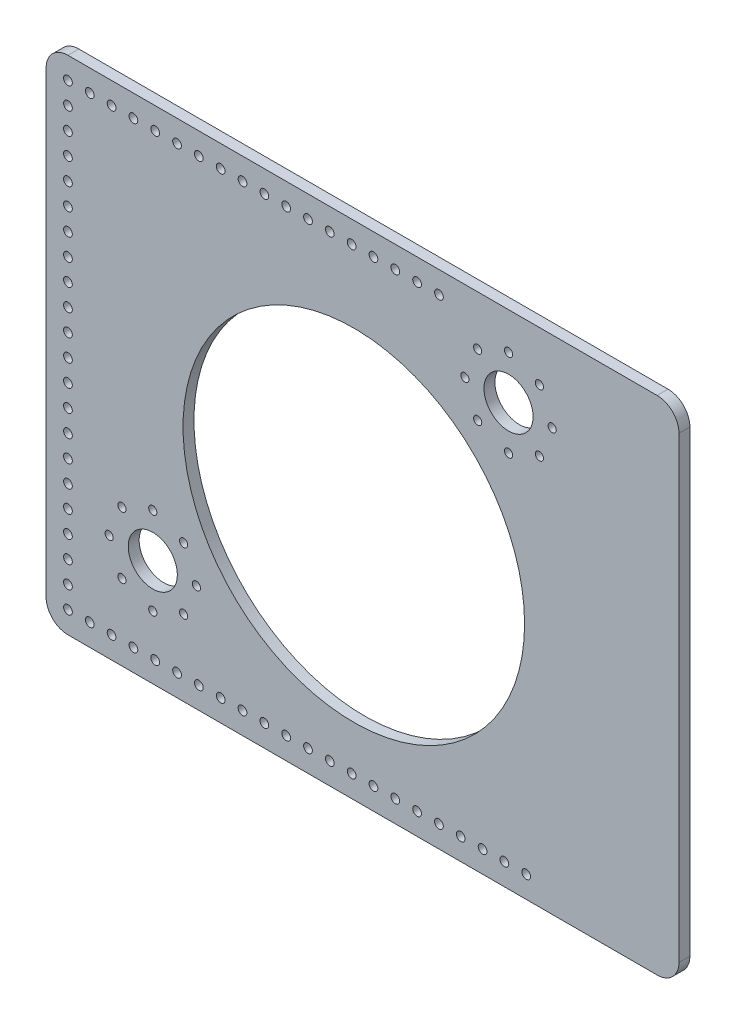
SolidWorks part; units mm, degrees
material "PC High Viscosity"
ref_plane "Front Plane" through (0, 0, 0) normal (0, 0, 1) x (1, 0, 0)
ref_plane "Top Plane" through (0, 0, 0) normal (0, 1, 0) x (1, 0, 0)
ref_plane "Right Plane" through (0, 0, 0) normal (1, 0, 0) x (0, 0, -1)
sketch "Sketch1" plane through (0, 0, 0) normal (0, 0, 1) x (1, 0, 0)
  line L1 (0, 0) -> (368.3, 0)
  line L2 (0, 0) -> (0, 292.1)
  line L4 (368.3, 0) -> (368.3, 292.1)
  line L5 (0, 292.1) -> (368.3, 292.1)
  circle A0 centre (179.07, 138.43) radius 99.3775
  circle A1 centre (12.7, 279.4) radius 2.54
  circle A2 centre (25.4, 279.4) radius 2.54
  circle A3 centre (38.1, 279.4) radius 2.54
  circle A4 centre (50.8, 279.4) radius 2.54
  circle A5 centre (63.5, 279.4) radius 2.54
  circle A6 centre (76.2, 279.4) radius 2.54
  circle A7 centre (88.9, 279.4) radius 2.54
  circle A8 centre (101.6, 279.4) radius 2.54
  circle A9 centre (114.3, 279.4) radius 2.54
  circle A10 centre (127, 279.4) radius 2.54
  circle A11 centre (139.7, 279.4) radius 2.54
  circle A12 centre (152.4, 279.4) radius 2.54
  circle A13 centre (165.1, 279.4) radius 2.54
  circle A14 centre (177.8, 279.4) radius 2.54
  circle A15 centre (190.5, 279.4) radius 2.54
  circle A16 centre (203.2, 279.4) radius 2.54
  circle A17 centre (215.9, 279.4) radius 2.54
  circle A18 centre (228.6, 279.4) radius 2.54
  circle A24 centre (12.7, 266.7) radius 2.54
  circle A25 centre (12.7, 254) radius 2.54
  circle A26 centre (12.7, 241.3) radius 2.54
  circle A27 centre (12.7, 228.6) radius 2.54
  circle A28 centre (12.7, 215.9) radius 2.54
  circle A29 centre (12.7, 203.2) radius 2.54
  circle A30 centre (12.7, 190.5) radius 2.54
  circle A31 centre (12.7, 177.8) radius 2.54
  circle A32 centre (12.7, 165.1) radius 2.54
  circle A33 centre (12.7, 152.4) radius 2.54
  circle A34 centre (12.7, 139.7) radius 2.54
  circle A35 centre (12.7, 127) radius 2.54
  circle A36 centre (12.7, 114.3) radius 2.54
  circle A37 centre (12.7, 101.6) radius 2.54
  circle A38 centre (12.7, 88.9) radius 2.54
  circle A39 centre (12.7, 76.2) radius 2.54
  circle A40 centre (12.7, 63.5) radius 2.54
  circle A41 centre (12.7, 50.8) radius 2.54
  circle A42 centre (12.7, 38.1) radius 2.54
  circle A43 centre (12.7, 25.4) radius 2.54
  circle A44 centre (12.7, 12.7) radius 2.54
  circle A45 centre (25.4, 12.7) radius 2.54
  circle A46 centre (38.1, 12.7) radius 2.54
  circle A47 centre (50.8, 12.7) radius 2.54
  circle A48 centre (63.5, 12.7) radius 2.54
  circle A49 centre (76.2, 12.7) radius 2.54
  circle A50 centre (88.9, 12.7) radius 2.54
  circle A51 centre (101.6, 12.7) radius 2.54
  circle A52 centre (114.3, 12.7) radius 2.54
  circle A53 centre (127, 12.7) radius 2.54
  circle A54 centre (139.7, 12.7) radius 2.54
  circle A55 centre (152.4, 12.7) radius 2.54
  circle A56 centre (165.1, 12.7) radius 2.54
  circle A57 centre (177.8, 12.7) radius 2.54
  circle A58 centre (190.5, 12.7) radius 2.54
  circle A59 centre (203.2, 12.7) radius 2.54
  circle A60 centre (215.9, 12.7) radius 2.54
  circle A61 centre (228.6, 12.7) radius 2.54
  circle A62 centre (241.3, 12.7) radius 2.54
  circle A63 centre (254, 12.7) radius 2.54
  circle A64 centre (266.7, 12.7) radius 2.54
  circle A65 centre (279.4, 12.7) radius 2.54
  dimension "D3" = 198.755
  dimension "D4" = 5.08
  dimension "D5" = 12.7
  dimension "D11" = 12.7
  dimension "D12" = 266.7
  dimension "D14" = 292.1
  dimension "D15" = 12.7
  dimension "D2" = 138.43
  dimension "D6" = 12.7
  dimension "D7" = 368.3
  dimension "D8" = 18
  dimension "D9" = 22
  dimension "D10" = 22
  dimension "D13" = 189.23
extrude "Boss-Extrude1" add sketch "Sketch1" along normal blind 6.35
sketch "Sketch2" plane through (0, 0, 6.35) normal (0, 0, 1) x (1, 0, 0)
  line L0 (177.2452, 140.4926) -> (-32620.0354, 37211.0747) construction
  line L1 (62.0797, 62.0797) -> (0, 62.0797) construction
  line L2 (62.0797, 62.0797) -> (62.0797, 0) construction
  line L3 (62.0797, 0) -> (0, 0) construction
  line L4 (0, 62.0797) -> (0, 0) construction
  line L5 (368.3, 292.1) -> (0, 292.1) construction
  circle A0 centre (62.0797, 62.0797) radius 14.2875
  circle A2 centre (179.07, 138.43) radius 127 construction
  circle A4 centre (62.0797, 62.0797) radius 12.7 construction
  circle A5 centre (269.1087, 245.2435) radius 14.2875
  circle A6 centre (62.0797, 62.0797) radius 25.4 construction
  circle A7 centre (62.0797, 87.4797) radius 2.3812
  circle A8 centre (80.0402, 80.0402) radius 2.3813
  circle A9 centre (87.4797, 62.0797) radius 2.3813
  circle A10 centre (80.0402, 44.1192) radius 2.3813
  circle A11 centre (62.0797, 36.6797) radius 2.3812
  circle A12 centre (44.1192, 44.1192) radius 2.3812
  circle A13 centre (36.6797, 62.0797) radius 2.3812
  circle A14 centre (44.1192, 80.0402) radius 2.3812
  circle A15 centre (269.1087, 245.2435) radius 25.4 construction
  circle A16 centre (269.1087, 270.6435) radius 2.3813
  circle A17 centre (287.0692, 263.204) radius 2.3813
  circle A18 centre (294.5087, 245.2435) radius 2.3813
  circle A19 centre (287.0692, 227.283) radius 2.3813
  circle A20 centre (269.1087, 219.8435) radius 2.3813
  circle A21 centre (251.1482, 227.283) radius 2.3813
  circle A22 centre (243.7087, 245.2435) radius 2.3813
  circle A23 centre (251.1482, 263.204) radius 2.3813
  point P36 (62.0797, 62.0797)
  point P54 (269.1087, 245.2435)
  dimension "D1" = 28.575
  dimension "D2" = 139.7
  dimension "D3" = 254
  dimension "D4" = 25.4
  dimension "D6" = 50.8
  dimension "D7" = 4.7625
  dimension "D9" = 4.7625
  dimension "D5" = 48.5
  dimension "D8" = 8
  dimension "D10" = 8
extrude "Cut-Extrude1" cut sketch "Sketch2" against normal through all
fillet "Fillet1" radius 12.7 4 edges at (0, 0, 3.175) (0, 292.1, 3.175) (368.3, 292.1, 3.175) (368.3, 0, 3.175)
